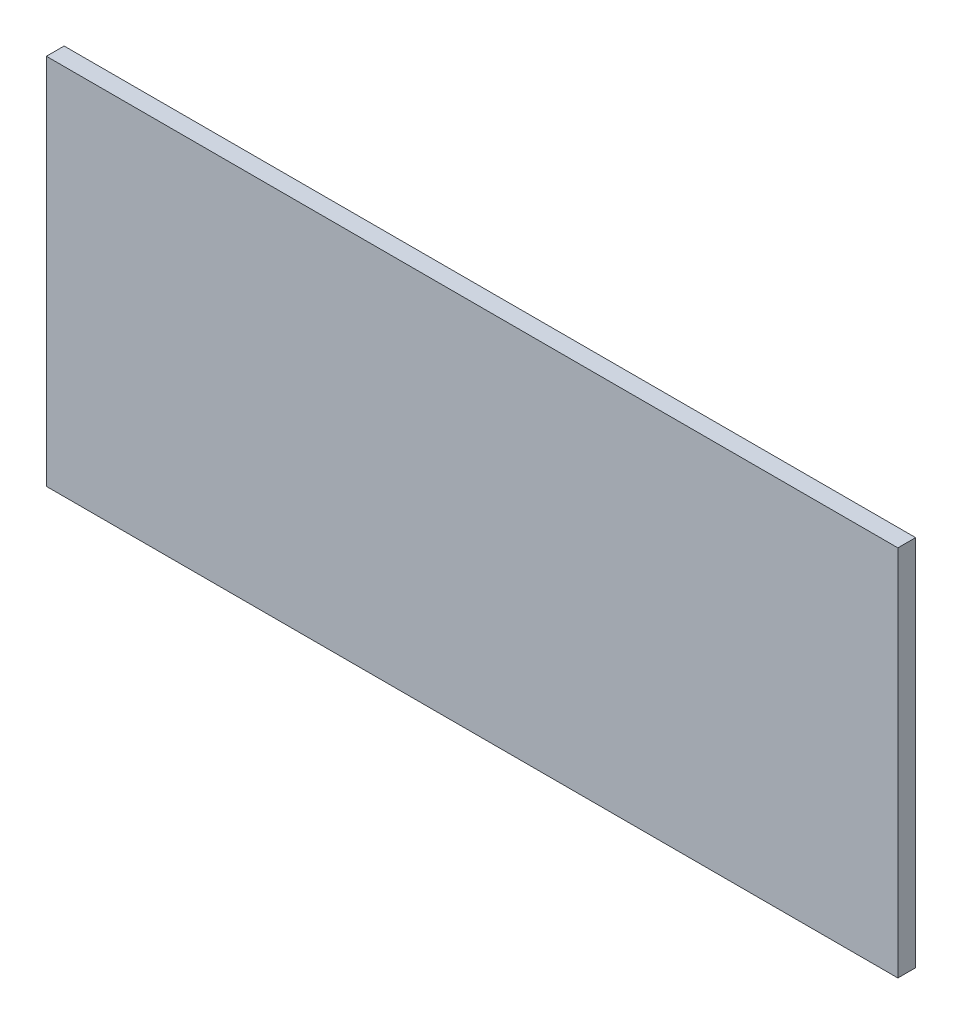
SolidWorks part; units mm, degrees
ref_plane "Plan de face" through (0, 0, 0) normal (0, 0, 1) x (1, 0, 0)
ref_plane "Plan de dessus" through (0, 0, 0) normal (0, 1, 0) x (1, 0, 0)
ref_plane "Plan de droite" through (0, 0, 0) normal (1, 0, 0) x (0, 0, -1)
sketch "Esquisse1" plane through (0, 0, 0) normal (0, 0, 1) x (1, 0, 0)
  line L1 (-290, 105) -> (190, 105)
  line L2 (-290, 105) -> (-290, -105)
  line L3 (-290, -105) -> (190, -105)
  line L4 (190, 105) -> (190, -105)
  dimension "D1" = 480
  dimension "D2" = 210
  dimension "D3" = 105
  dimension "D4" = 190
extrude "Boss.-Extru.1" add sketch "Esquisse1" along normal blind 10
